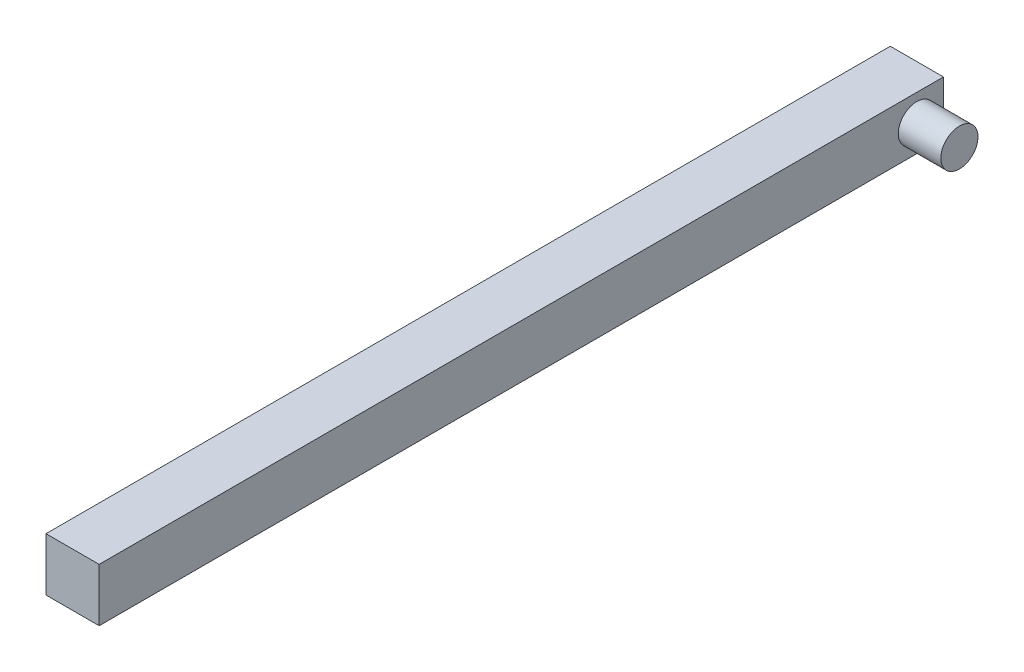
SolidWorks part; units mm, degrees
ref_plane "Front Plane" through (0, 0, 0) normal (0, 0, 1) x (1, 0, 0)
ref_plane "Top Plane" through (0, 0, 0) normal (0, 1, 0) x (1, 0, 0)
ref_plane "Right Plane" through (0, 0, 0) normal (1, 0, 0) x (0, 0, -1)
sketch "Sketch2" plane through (0, 0, 0) normal (0, 0, 1) x (1, 0, 0)
  line L1 (0, 0) -> (10, 0)
  line L2 (0, 0) -> (0, 10)
  line L3 (0, 10) -> (10, 10)
  line L4 (10, 0) -> (10, 10)
  dimension "D1" = 10
  dimension "D2" = 10
extrude "Boss-Extrude1" add sketch "Sketch2" along normal blind 158.8
sketch "Sketch3" plane through (10, 0, 0) normal (1, 0, 0) x (0, 0, -1)
  line L0 (0, 0) -> (0, 10) construction
  line L1 (-158.8, 10) -> (0, 10) construction
  circle A0 centre (-5, 5) radius 3.5
  dimension "D3" = 7
  dimension "D1" = 5
  dimension "D2" = 5
extrude "Boss-Extrude2" add sketch "Sketch3" along normal blind 8
sketch "Sketch4" plane through (0, 0, 158.8) normal (0, 0, 1) x (1, 0, 0)
  line L0 (0, 18.97) -> (0, -8.97)
  line L1 (0, -8.97) -> (15, -8.97)
  line L2 (15, -8.97) -> (15, 18.97)
  line L3 (15, 18.97) -> (0, 18.97)
  line L4 (0, 0) -> (10, 0) construction
  line L7 (10, 0) -> (10, 10) construction
  dimension "D1" = 270
  dimension "D2" = 27.94
  dimension "D3" = 10
  dimension "D4" = 8.97
  dimension "D5" = 15
extrude "Boss-Extrude4" add sketch "Sketch4" along normal blind 4
sketch "Sketch5" plane through (0, 0, 162.8) normal (0, 0, 1) x (1, 0, 0)
  line L0 (0, -8.97) -> (15, -8.97) construction
  line L1 (15, 18.97) -> (12.7455, 18.97)
  line L2 (15, 18.97) -> (15, -8.97)
  line L3 (15, -8.97) -> (12.7455, -8.97)
  line L4 (12.7455, 18.97) -> (12.7455, -8.97)
extrude "Boss-Extrude5" add sketch "Sketch5" along normal blind 4
sketch "Sketch6" plane through (12.7455, 0, 0) normal (-1, 0, 0) x (0, 0, 1)
  line L0 (162.8, 18.97) -> (162.8, -8.97) construction
  line L2 (166.8, -8.97) -> (162.8, -8.97) construction
  circle A0 centre (165.086, 16.6443) radius 1.5
  circle A1 centre (165.086, -6.645) radius 1.5
  dimension "D1" = 3
  dimension "D2" = 3
  dimension "D3" = 2.286
  dimension "D4" = 2.286
  dimension "D5" = 23.2893
  dimension "D6" = 2.325
extrude "Cut-Extrude1" cut sketch "Sketch6" against normal blind 40
sketch "Sketch7" plane through (0, 0, 166.8) normal (0, 0, 1) x (1, 0, 0)
  line L1 (15, -8.97) -> (0, -8.97)
  line L2 (15, -8.97) -> (15, 18.97)
  line L3 (15, 18.97) -> (0, 18.97)
  line L4 (0, -8.97) -> (0, 18.97)
extrude "Cut-Extrude2" cut sketch "Sketch7" against normal up to surface (8 mm away) up to face at (6.25, 5, 158.8)
